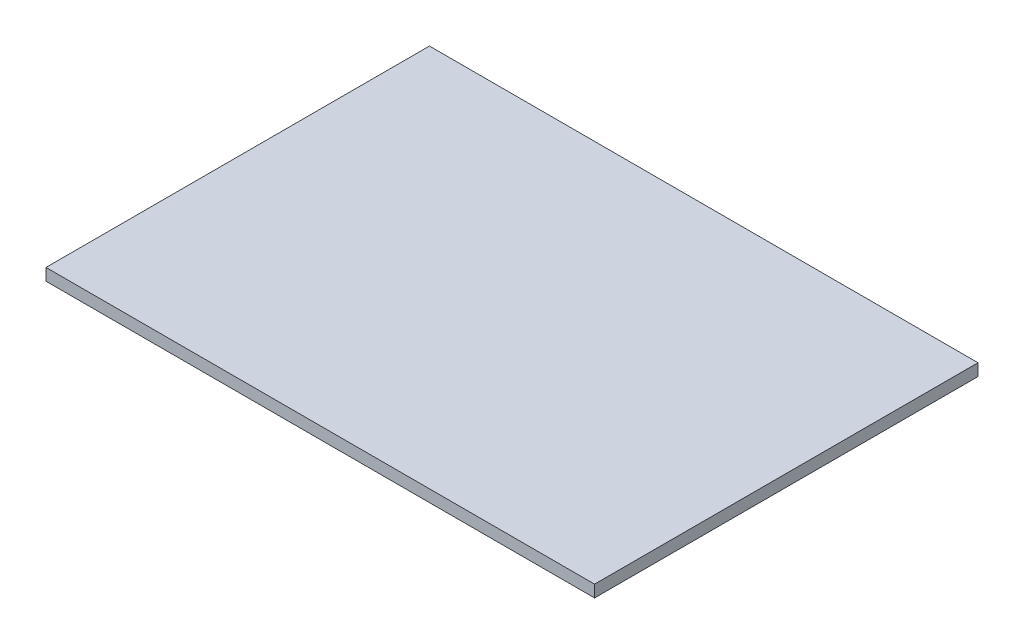
SolidWorks part; units mm, degrees
material "Acrylic (Medium-high impact)"
ref_plane "Front Plane" through (0, 0, 0) normal (0, 0, 1) x (1, 0, 0)
ref_plane "Top Plane" through (0, 0, 0) normal (0, 1, 0) x (1, 0, 0)
ref_plane "Right Plane" through (0, 0, 0) normal (1, 0, 0) x (0, 0, -1)
sketch "Sketch1" plane through (0, 0, 0) normal (0, 1, 0) x (1, 0, 0)
  line L0 (39.8521, -10.733) -> (39.8521, -137.733) construction
  line L1 (-32.8229, -10.733) -> (39.8521, -10.733)
  line L2 (-32.8229, -10.733) -> (-32.8229, -61.533)
  line L3 (-32.8229, -61.533) -> (39.8521, -61.533)
  line L4 (39.8521, -10.733) -> (39.8521, -61.533)
  line L5 (-32.8229, -10.733) -> (-32.8229, -137.733) construction
  line L6 (38.2646, -10.733) -> (-31.2354, -10.733) construction
  line L7 (39.8521, -10.733) -> (39.8521, -137.733) construction
  line L8 (-32.8229, -10.733) -> (-32.8229, -137.733) construction
  line L9 (38.2646, -10.733) -> (-31.2354, -10.733) construction
  dimension "D1" = 50.8
extrude "Boss-Extrude1" add sketch "Sketch1" along normal blind 1.5875
